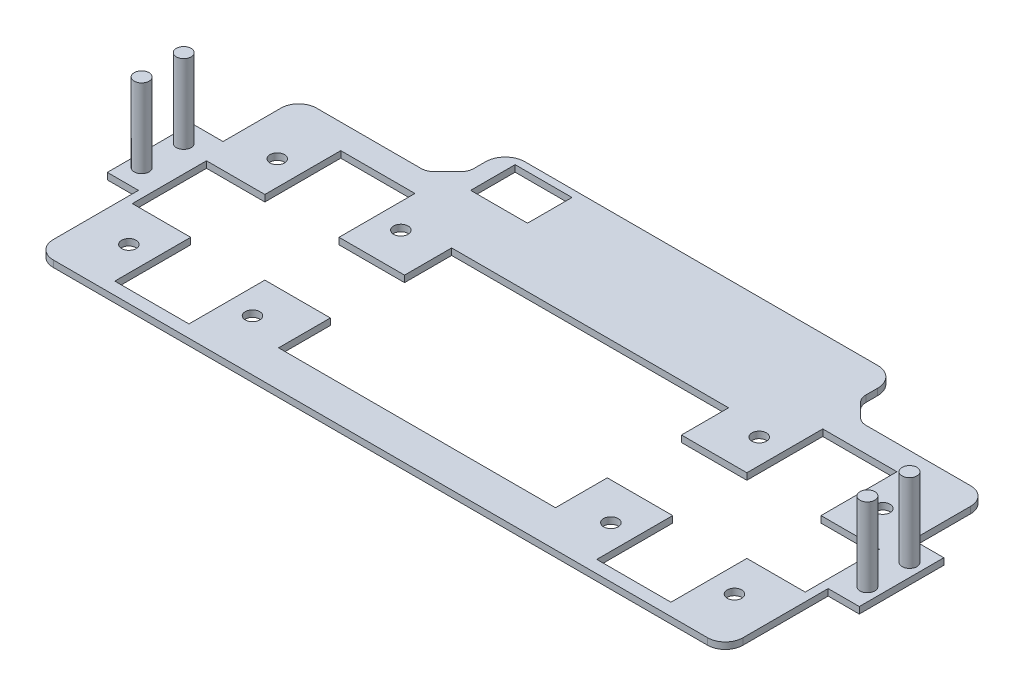
SolidWorks part; units mm, degrees
ref_plane "Front Plane" through (0, 0, 0) normal (0, 0, 1) x (1, 0, 0)
ref_plane "Top Plane" through (0, 0, 0) normal (0, 1, 0) x (1, 0, 0)
ref_plane "Right Plane" through (0, 0, 0) normal (1, 0, 0) x (0, 0, -1)
sketch "Sketch1" plane through (0, 0, 0) normal (0, 1, 0) x (1, 0, 0)
  line L0 (-179.1667, 134.5) -> (184.1667, 134.5) construction
  line L1 (0, 0) -> (0, 9.0935)
  line L2 (0, 9.0935) -> (-247.6771, 9.0935)
  line L3 (-261.1771, 22.5935) -> (-261.1771, 196.3977)
  line L4 (-247.6771, 209.8977) -> (-167.7492, 209.8977)
  line L5 (-160.6781, 212.8266) -> (-150.5689, 222.9358)
  line L6 (-147.64, 230.0069) -> (-147.64, 238.9611)
  line L8 (0, 253.9611) -> (-132.64, 253.9611)
  line L9 (0, 9.0935) -> (3.9629, 9.0935)
  line L10 (265.1401, 152.2077) -> (288.9657, 152.2077)
  line L11 (-261.1771, 87.5935) -> (-285.0028, 87.5935)
  line L12 (1.9815, 9.0935) -> (1.9815, 14.4532)
  line L13 (3.9629, 9.0935) -> (251.6401, 9.0935)
  line L14 (265.1401, 22.5935) -> (265.1401, 196.3977)
  line L15 (251.6401, 209.8977) -> (171.7121, 209.8977)
  line L16 (164.6411, 212.8266) -> (154.5319, 222.9358)
  line L17 (151.6029, 230.0069) -> (151.6029, 238.9611)
  line L18 (3.9629, 253.9611) -> (136.6029, 253.9611)
  line L19 (0, 253.9611) -> (3.9629, 253.9611)
  line L21 (-261.1771, 152.2077) -> (-285.0028, 152.2077)
  line L22 (-285.0028, 87.5935) -> (-285.0028, 152.2077)
  line L23 (288.9657, 87.5935) -> (288.9657, 152.2077)
  line L24 (265.1401, 87.5935) -> (288.9657, 87.5935)
  line L25 (0, 9.0935) -> (3.9629, 9.0935)
  arc A0 (-247.6771, 9.0935) -> (-261.1771, 22.5935) centre (-247.6771, 22.5935) cw
  arc A1 (-247.6771, 209.8977) -> (-261.1771, 196.3977) centre (-247.6771, 196.3977) ccw
  arc A2 (-160.6781, 212.8266) -> (-167.7492, 209.8977) centre (-167.7492, 219.8977) cw
  arc A3 (-150.5689, 222.9358) -> (-147.64, 230.0069) centre (-157.64, 230.0069) ccw
  arc A4 (-132.64, 253.9611) -> (-147.64, 238.9611) centre (-132.64, 238.9611) ccw
  arc A5 (251.6401, 9.0935) -> (265.1401, 22.5935) centre (251.6401, 22.5935) ccw
  arc A6 (251.6401, 209.8977) -> (265.1401, 196.3977) centre (251.6401, 196.3977) cw
  arc A7 (164.6411, 212.8266) -> (171.7121, 209.8977) centre (171.7121, 219.8977) ccw
  arc A8 (154.5319, 222.9358) -> (151.6029, 230.0069) centre (161.6029, 230.0069) cw
  arc A9 (136.6029, 253.9611) -> (151.6029, 238.9611) centre (136.6029, 238.9611) cw
  point P45 (-273.0899, 87.5935)
  dimension "D1" = 13.5
  dimension "D2" = 13.5
  dimension "D3" = 10
  dimension "D4" = 10
  dimension "D5" = 15
  dimension "D6" = 65
extrude "Boss-Extrude1" add sketch "Sketch1" along normal blind 5
sketch "Sketch4" plane through (0, 5, 0) normal (0, 1, 0) x (1, 0, 0)
  line L1 (-258.6771, 110.9977) -> (-246.6771, 110.9977)
  line L2 (-258.6771, 110.9977) -> (-258.6771, 122.9977)
  line L3 (-258.6771, 122.9977) -> (-246.6771, 122.9977)
  line L4 (-246.6771, 110.9977) -> (-246.6771, 122.9977)
  line L5 (-258.6771, 110.9977) -> (-246.6771, 122.9977) construction
  line L6 (-258.6771, 122.9977) -> (-246.6771, 110.9977) construction
  line L7 (-247.6771, 209.8977) -> (-167.7492, 209.8977) construction
  line L8 (-261.1771, 22.5935) -> (-261.1771, 196.3977) construction
  point P0 (-252.6771, 116.9977)
  dimension "D1" = 12
  dimension "D2" = 12
  dimension "D3" = 86.9
  dimension "D4" = 2.5
scale "Scale2" scale about origin uniform scaling yes scale factor 0.265
sketch "Sketch5" plane through (0, 1.325, 0) normal (0, 1, 0) x (1, 0, 0)
  line L0 (-67.5119, 27.7729) -> (-31.4634, 27.7729)
  line L1 (-67.5119, 20.2729) -> (-55.7119, 20.2729)
  line L2 (-67.5119, 20.2729) -> (-67.5119, 35.2729)
  line L3 (-67.5119, 35.2729) -> (-55.7119, 35.2729)
  line L5 (-67.5119, 20.2729) -> (-53.5663, 29.7486) construction
  line L6 (-67.5119, 35.2729) -> (-52.3036, 24.9392) construction
  line L7 (-65.6344, 55.6229) -> (-44.4535, 55.6229) construction
  line L8 (-48.2119, 35.6229) -> (-48.2119, 22.877)
  line L9 (-55.7119, 50.6229) -> (-55.7119, 35.2729)
  line L11 (-40.7119, 35.2729) -> (-40.7119, 35.6229)
  line L13 (-55.7119, 4.9229) -> (-55.7119, 20.2729)
  line L14 (-69.2119, 5.9873) -> (-69.2119, 52.0454) construction
  line L15 (-55.7119, 4.9229) -> (-40.7119, 4.9229)
  line L18 (-55.7119, 50.6229) -> (-40.7119, 50.6229)
  line L19 (-40.7119, 35.6229) -> (-40.7119, 50.6229)
  line L20 (-55.7119, 35.6229) -> (-40.7119, 50.6229) construction
  line L21 (-55.7119, 50.6229) -> (-40.7119, 35.6229) construction
  line L22 (-40.7119, 19.9229) -> (-40.7119, 4.9229)
  line L23 (-40.7119, 20.2729) -> (-40.7119, 19.9229)
  line L24 (-28.9119, 35.2729) -> (-40.7119, 35.2729)
  line L26 (-28.9119, 20.2729) -> (-40.7119, 20.2729)
  line L28 (0.5251, 2.4098) -> (0.5251, 2.9656)
  line L29 (66.6846, 2.4098) -> (-65.6344, 2.4098) construction
  line L30 (68.5621, 20.2729) -> (68.5621, 35.2729)
  line L31 (68.5621, 35.2729) -> (56.7621, 35.2729)
  line L32 (56.7621, 50.6229) -> (56.7621, 35.2729)
  line L33 (56.7621, 50.6229) -> (41.7621, 50.6229)
  line L34 (41.7621, 35.6229) -> (41.7621, 50.6229)
  line L35 (41.7621, 35.2729) -> (41.7621, 35.6229)
  line L36 (29.9621, 35.2729) -> (41.7621, 35.2729)
  line L38 (29.9621, 20.2729) -> (41.7621, 20.2729)
  line L39 (41.7621, 20.2729) -> (41.7621, 19.9229)
  line L40 (41.7621, 19.9229) -> (41.7621, 4.9229)
  line L41 (56.7621, 4.9229) -> (41.7621, 4.9229)
  line L42 (56.7621, 4.9229) -> (56.7621, 20.2729)
  line L43 (68.5621, 20.2729) -> (56.7621, 20.2729)
  line L44 (-35.1496, 67.2997) -> (36.1998, 67.2997) construction
  line L45 (-24.1246, 56.7997) -> (-35.6246, 56.7997)
  line L46 (-24.1246, 56.7997) -> (-24.1246, 65.7997)
  line L47 (-24.1246, 65.7997) -> (-35.6246, 65.7997)
  line L48 (-35.6246, 56.7997) -> (-35.6246, 65.7997)
  line L49 (-24.1246, 56.7997) -> (-35.6246, 65.7997) construction
  line L50 (-24.1246, 65.7997) -> (-35.6246, 56.7997) construction
  line L51 (-39.1246, 60.9518) -> (-39.1246, 63.3247) construction
  line L52 (-27.4619, 9.7997) -> (28.5381, 9.7997)
  line L53 (-27.4619, 9.7997) -> (-27.4619, 20.2729)
  line L54 (-27.4619, 44.7997) -> (28.5381, 44.7997)
  line L55 (28.5381, 9.7997) -> (28.5381, 20.2729)
  line L56 (-27.4619, 9.7997) -> (28.5381, 44.7997) construction
  line L57 (-27.4619, 44.7997) -> (28.5381, 9.7997) construction
  line L58 (-28.9119, 35.2729) -> (-27.4619, 35.2729)
  line L59 (70.2621, 5.9873) -> (70.2621, 52.0454) construction
  line L60 (-27.4619, 35.2729) -> (-27.4619, 44.7997)
  line L61 (28.5381, 35.2729) -> (28.5381, 44.7997)
  line L62 (-28.9119, 20.2729) -> (-27.4619, 20.2729)
  line L63 (28.5381, 20.2729) -> (29.9621, 20.2729)
  line L64 (28.5381, 35.2729) -> (29.9621, 35.2729)
  circle A0 centre (-35.7119, 42.7729) radius 1.4685
  circle A1 centre (-60.7119, 42.7729) radius 1.4685
  circle A2 centre (-60.7119, 12.7729) radius 1.4685
  circle A3 centre (-35.7119, 12.7729) radius 1.4685
  circle A4 centre (36.7621, 12.7729) radius 1.4685
  circle A5 centre (61.7621, 12.7729) radius 1.4685
  circle A6 centre (36.7621, 42.7729) radius 1.4685
  circle A7 centre (61.7621, 42.7729) radius 1.4685
  point P0 (-56.474, 27.7729)
  point P9 (-48.2119, 43.1229)
  point P14 (-48.2119, 50.6229)
  point P48 (-29.8746, 61.2997)
  point P58 (0.5381, 27.2997)
  point P82 (0, 0)
  dimension "D17" = 7.5
  dimension "D1" = 15
  dimension "D2" = 15
  dimension "D3" = 20.35
  dimension "D4" = 1.7
  dimension "D5" = 15
  dimension "D6" = 15
  dimension "D7" = 5
  dimension "D8" = 13.5
  dimension "D9" = 11.5
  dimension "D10" = 9
  dimension "D11" = 1.5
  dimension "D12" = 3.5
  dimension "D13" = 35
  dimension "D14" = 56
  dimension "D15" = 22.5
  dimension "D16" = 69.75
  dimension "D18" = 90
  dimension "D19" = 5
sketch "Sketch6" plane through (0, 1.325, 0) normal (0, 1, 0) x (1, 0, 0)
  line L0 (-69.2119, 5.9873) -> (-69.2119, 52.0454) construction
  line L1 (-69.2119, 23.2123) -> (-75.5119, 23.2123)
  line L2 (-69.2119, 23.2123) -> (-69.2119, 40.3123)
  line L3 (-69.2119, 40.3123) -> (-75.5119, 40.3123)
  line L4 (-75.5119, 23.2123) -> (-75.5119, 40.3123)
  line L5 (70.2621, 5.9873) -> (70.2621, 52.0454) construction
  line L6 (70.2621, 23.2123) -> (76.5621, 23.2123)
  line L7 (70.2621, 23.2123) -> (70.2621, 40.3123)
  line L8 (70.2621, 40.3123) -> (76.5621, 40.3123)
  line L9 (76.5621, 23.2123) -> (76.5621, 40.3123)
  dimension "D1" = 17.1
  dimension "D2" = 6.3
  dimension "D3" = 6.3
  dimension "D4" = 17.1
  dimension "D5" = 17.225
  dimension "D6" = 17.225
extrude "Boss-Extrude2" add sketch "Sketch6" against normal blind 1.325
extrude "Cut-Extrude1" cut sketch "Sketch5" against normal blind 1.325
sketch "Sketch8" plane through (0, 1.325, 0) normal (0, 1, 0) x (1, 0, 0)
  line L0 (-75.5119, 40.3123) -> (-75.5119, 23.2123) construction
  line L1 (-69.2119, 40.3123) -> (-75.5119, 40.3123) construction
  line L2 (-75.5119, 23.2123) -> (-69.2119, 23.2123) construction
  line L3 (0.5251, 2.4098) -> (0.5251, 3.5279)
  line L4 (66.6846, 2.4098) -> (-65.6344, 2.4098) construction
  circle A0 centre (-72.8619, 36.0193) radius 1.5
  circle A1 centre (-72.8619, 27.5053) radius 1.5
  circle A2 centre (73.9121, 36.0193) radius 1.5
  circle A3 centre (73.9121, 27.5053) radius 1.5
  point P18 (0, 0)
  dimension "D1" = 3
  dimension "D2" = 3
  dimension "D3" = 2.65
  dimension "D4" = 2.65
  dimension "D5" = 4.293
  dimension "D6" = 4.293
extrude "Boss-Extrude5" add sketch "Sketch8" along normal blind 15.9 contours A0 | A1 | A2 | A3
